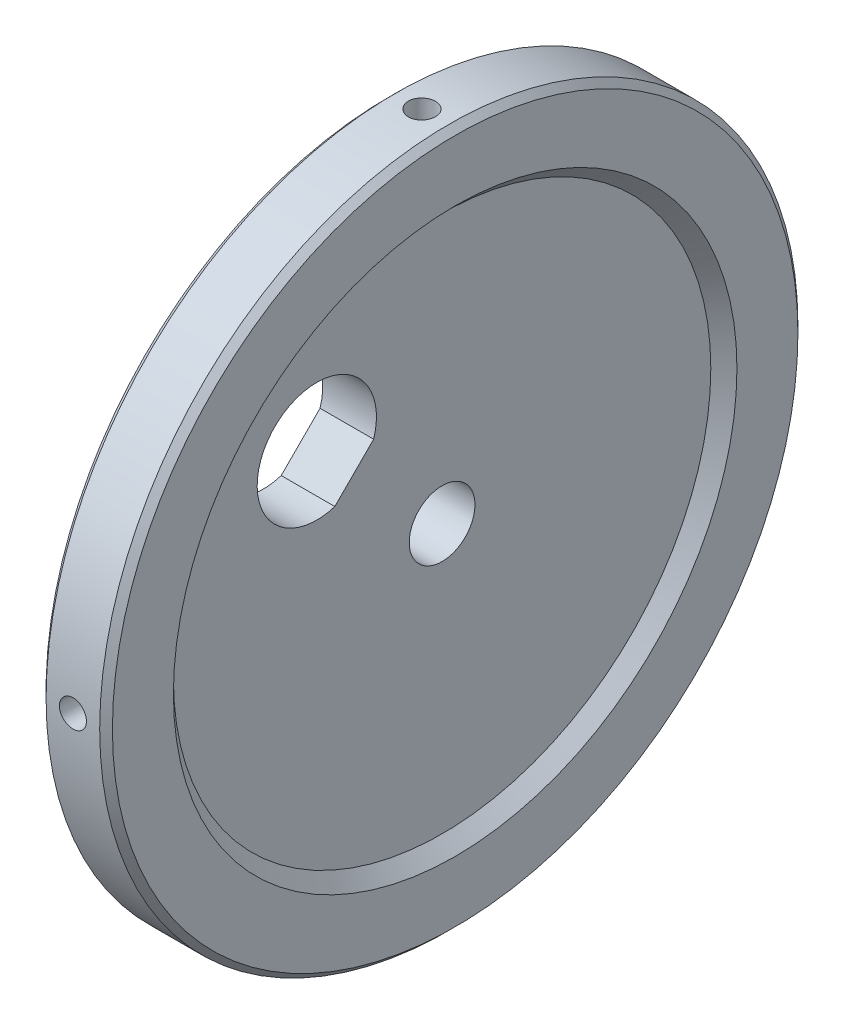
SolidWorks part; units mm, degrees
ref_plane "Front Plane" through (0, 0, 0) normal (0, 0, 1) x (1, 0, 0)
ref_plane "Top Plane" through (0, 0, 0) normal (0, 1, 0) x (1, 0, 0)
ref_plane "Right Plane" through (0, 0, 0) normal (1, 0, 0) x (0, 0, -1)
sketch "Sketch1" plane through (0, 0, 0) normal (0, 1, 0) x (1, 0, 0)
  line L1 (0, -55) -> (0, 55) construction
  line L2 (0, 4.9022) -> (0, 52.0992)
  line L3 (0, 52.0992) -> (10, 52.0992)
  line L4 (10, 52.0992) -> (10, 42.0992)
  line L8 (8, 4.9022) -> (8, 40.0992)
  line L9 (8, 40.0992) -> (10, 42.0992)
  line L10 (0, 4.9022) -> (8, 4.9022)
  dimension "D1" = 225
  dimension "D2" = 47.197
  dimension "D3" = 10
  dimension "D4" = 10
  dimension "D5" = 8
sketch "Sketch2" plane through (0, 0, 0) normal (0, 1, 0) x (1, 0, 0)
  line L0 (0, 0) -> (9.8109, 0)
  line L1 (-5.5, 0) -> (5.5, 0) construction
revolve "Revolve1" add sketch "Sketch1" angle 360 about L0
sketch "Sketch3" plane through (8, 0, 0) normal (1, 0, 0) x (0, 0, -1)
  line L6 (-16.0121, 10.2156) -> (-10.2156, 16.0121)
  arc A1 (-24.9933, 24.9933) -> (-10.2156, 16.0121) centre (-18.7, 18.7) cw
  arc A2 (-24.9933, 24.9933) -> (-16.0121, 10.2156) centre (-18.7, 18.7) ccw
extrude "Cut-Extrude1" cut sketch "Sketch3" against normal blind 10
ref_plane "Plane1" through (0, 0, 52.0992) normal (0, 0, 1) x (1, 0, 0)
sketch "Sketch4" plane through (0, 0, 52.0992) normal (0, 0, 1) x (1, 0, 0)
  line L0 (0, 0) -> (5, 0)
  line L1 (5.5, 0) -> (-5.5, 0) construction
  dimension "D1" = 5
hole_wizard "#10-32 Tapped Hole1" positions "Sketch5" profile "Sketch6" tap size "#10-32" standard "ANSI Inch"
sketch "Sketch5" plane through (0, 0, 52.0992) normal (0, 0, 1) x (1, 0, 0)
  point P0 (5, 0)
sketch "Sketch6" plane through (5, 0, 52.0992) normal (1, 0, 0) x (0, -1, 0)
  line L0 (0, 0) -> (0, 9.7133)
  line L1 (0, 9.7133) -> (2.0193, 8.5)
  line L2 (2.0193, 8.5) -> (2.0193, 0)
  line L5 (2.0193, 0) -> (0, 0)
  line L10 (0, 9.7133) -> (-2.0193, 8.5) construction
  line L11 (0, -6.35) -> (0, 107.95) construction
  dimension "Tap Drill Dia." = 4.0386
  dimension "Tap Drill Depth" = 8.5
  dimension "Drill Angle" = 118
cosmetic thread "Hole Thread1" parameters "D1"=8.5, "D2"=4.826
pattern_circular "CirPattern2" count 4 over 360 of "#10-32 Tapped Hole1"
cosmetic thread "Hole Thread2" parameters "D1"=8.5, "D2"=4.826
cosmetic thread "Hole Thread3" parameters "D1"=8.5, "D2"=4.826
cosmetic thread "Hole Thread4" parameters "D1"=8.5, "D2"=4.826
chamfer "Chamfer1" distance 1 angle 45 1 edges at (10, 0, 52.0992)
chamfer "Chamfer2" distance 1 angle 45 1 edges at (0, 0, 52.0992)
sketch "Sketch8" plane through (10, 0, 0) normal (1, 0, 0) x (0, 0, -1)
  circle A0 centre (0, 0) radius 52.0992
extrude "Cut-Extrude2" cut sketch "Sketch8" against normal blind 0.0508
